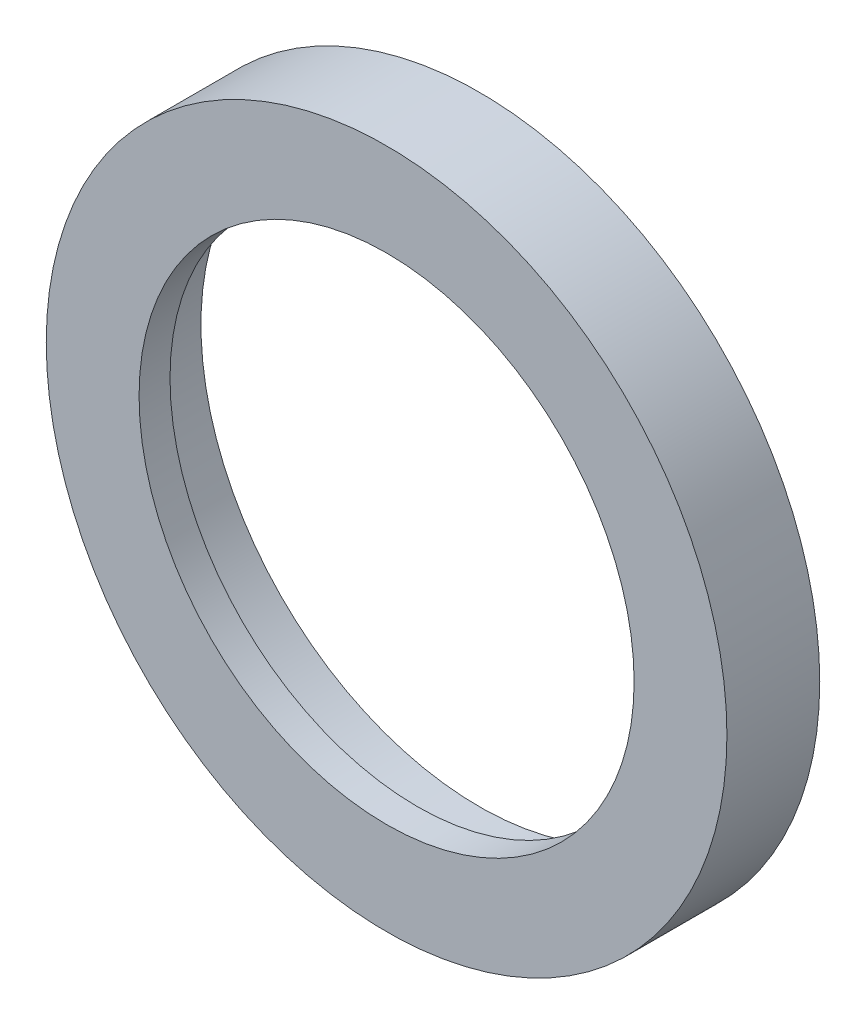
SolidWorks part; units mm, degrees
ref_plane "Front Plane" through (0, 0, 0) normal (0, 0, 1) x (1, 0, 0)
ref_plane "Top Plane" through (0, 0, 0) normal (0, 1, 0) x (1, 0, 0)
ref_plane "Right Plane" through (0, 0, 0) normal (1, 0, 0) x (0, 0, -1)
sketch "Sketch1" plane through (0, 0, 0) normal (1, 0, 0) x (0, 0, -1)
  line L0 (0, 0) -> (58.2474, 0) construction
  line L1 (0, 16) -> (0, 22)
  line L2 (0, 22) -> (6, 22)
  line L3 (6, 22) -> (6, 18)
  line L4 (6, 18) -> (2, 18)
  line L5 (2, 18) -> (2, 16)
  line L6 (2, 16) -> (0, 16)
  line L7 (0, 0) -> (0, 12.2825) construction
  dimension "D1" = 6
  dimension "D2" = 2
  dimension "D3" = 2
  dimension "D4" = 4
  dimension "D5" = 44
revolve "Revolve1" add sketch "Sketch1" angle 360 about L0
